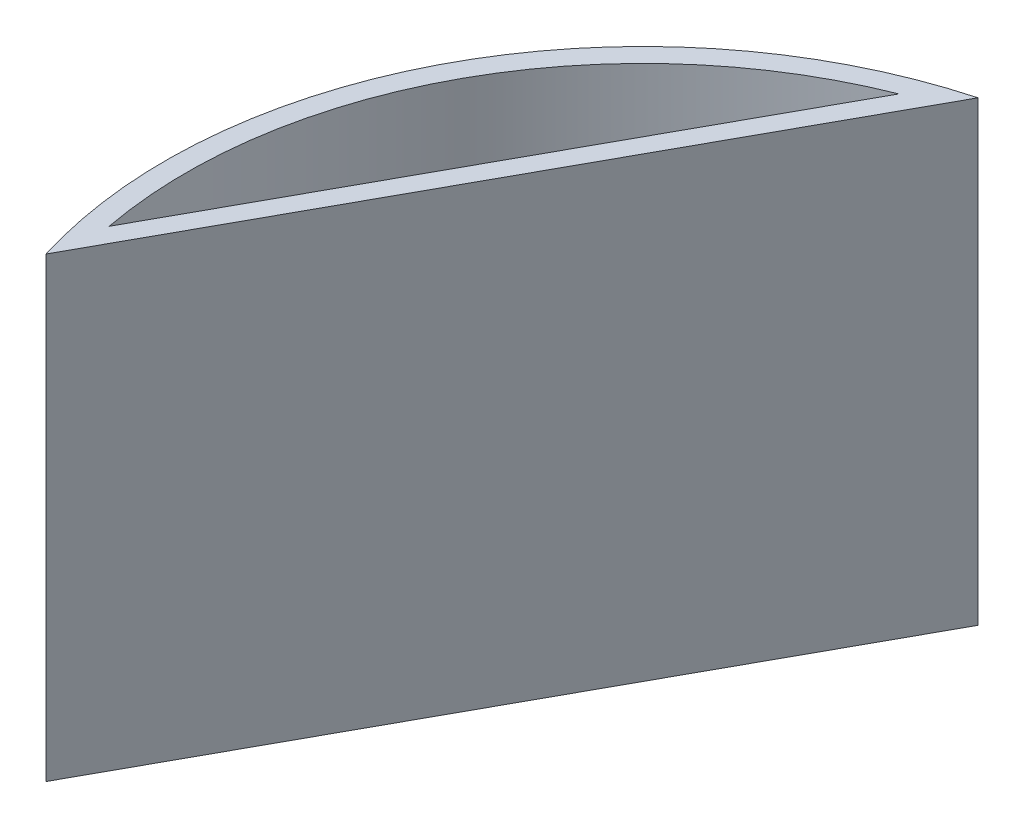
SolidWorks part; units mm, degrees
ref_plane "Front Plane" through (0, 0, 0) normal (0, 0, 1) x (1, 0, 0)
ref_plane "Top Plane" through (0, 0, 0) normal (0, 1, 0) x (1, 0, 0)
ref_plane "Right Plane" through (0, 0, 0) normal (1, 0, 0) x (0, 0, -1)
sketch "Sketch1" plane through (0, 0, 0) normal (0, 1, 0) x (1, 0, 0)
  circle A0 centre (0, 0) radius 69.85
  circle A1 centre (0, 0) radius 73.025
  dimension "D1" = 139.7
  dimension "D2" = 146.05
extrude "Boss-Extrude1" add sketch "Sketch1" along normal blind 63.5
sketch "Sketch2" plane through (0, 0, 0) normal (0, -1, 0) x (1, 0, 0)
  circle A0 centre (0, 0) radius 73.025
  dimension "D1" = 146.05
extrude "Boss-Extrude2" add sketch "Sketch2" along normal blind 6.35
sketch "Sketch3" plane through (0, 0, 0) normal (0, 1, 0) x (1, 0, 0)
  line L1 (-67.6153, -17.527) -> (-21.4092, 66.4881)
  circle A1 centre (0, 0) radius 69.85 construction
  arc A2 (-21.4092, 66.4881) -> (-67.6153, -17.527) centre (0, 0) ccw
  dimension "D1" = 50.8
extrude "Boss-Extrude3" add sketch "Sketch3" along normal blind 63.5
sketch "Sketch4" plane through (0, 63.5, 0) normal (0, 1, 0) x (1, 0, 0)
  line L0 (-25.7919, 64.9138) -> (-68.6329, -12.9827)
  line L1 (-67.6153, -17.527) -> (-21.4092, 66.4881) construction
  arc A0 (-25.7919, 64.9138) -> (-68.6329, -12.9827) centre (0, 0) ccw
  dimension "D2" = 69.85
  dimension "D1" = 88.9
extrude "Cut-Extrude2" cut sketch "Sketch4" against normal blind 57.15 and the other way blind 6.35 from offset 6.35 offset against normal yes
ref_plane "Plane1" through (-42.2867, 0, -23.2565) normal (0.8762, 0, 0.4819) x (0.4819, 0, -0.8762)
sketch "Sketch7" plane through (0, 63.5, 0) normal (0, 1, 0) x (1, 0, 0)
  line L0 (-72.6096, -26.608) -> (-10.1714, 86.9215)
  line L1 (-10.1714, 86.9215) -> (114.9599, 65.8058)
  line L2 (114.9599, 65.8058) -> (122.5488, -33.7487)
  line L3 (122.5488, -33.7487) -> (41.0179, -93.9807)
  line L4 (41.0179, -93.9807) -> (-75.6034, -72.6768)
  line L5 (-75.6034, -72.6768) -> (-72.6096, -26.608)
  line L6 (-67.6153, -17.527) -> (-21.4092, 66.4881) construction
extrude "Cut-Extrude5" cut sketch "Sketch7" against normal blind 1016
sketch "Sketch8" plane through (0, 63.5, 0) normal (0, 1, 0) x (1, 0, 0)
  line L0 (-38.5266, 42.2924) -> (-55.9883, 10.5424)
  line L1 (-55.9883, 10.5424) -> (-67.1163, 16.6625)
  line L2 (-67.1163, 16.6625) -> (-49.6547, 48.4125)
  line L3 (-49.6547, 48.4125) -> (-38.5266, 42.2924)
  line L4 (-69.7926, -21.4859) -> (-19.2319, 70.447) construction
  dimension "D1" = 31.75
  dimension "D2" = 12.7
extrude "Cut-Extrude6" [suppressed] cut sketch "Sketch8" against normal blind 6.35
